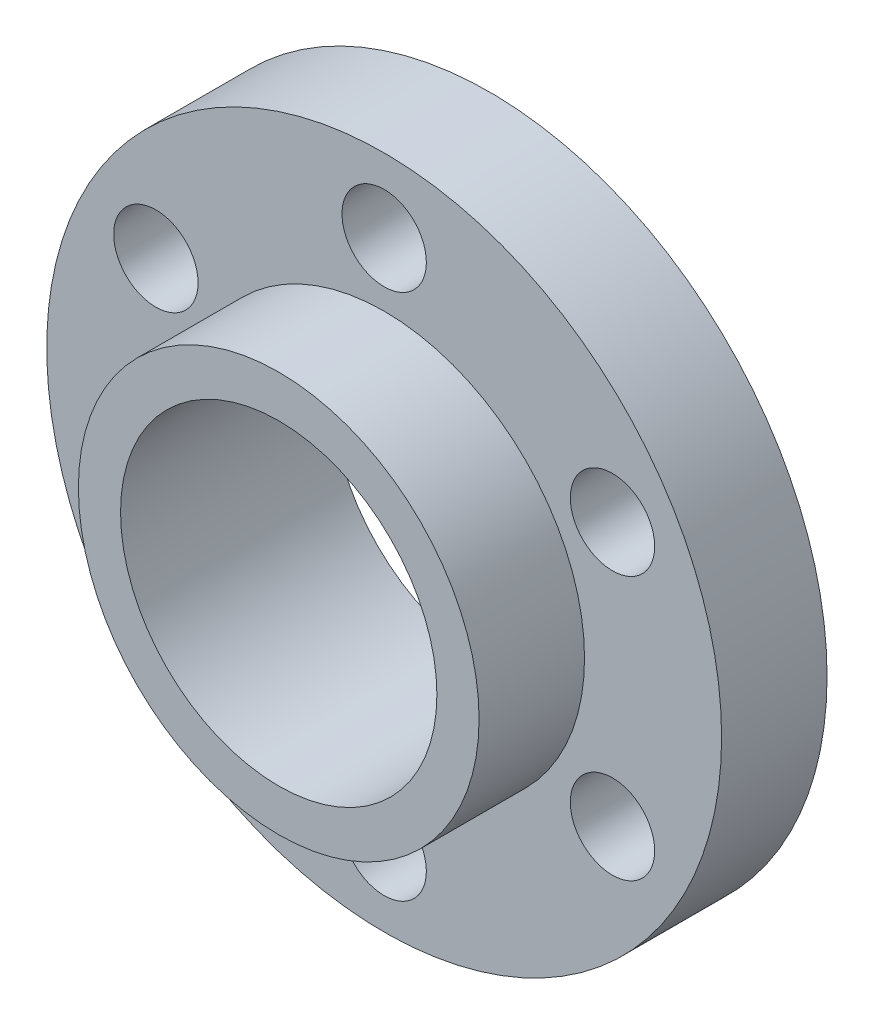
SolidWorks part; units mm, degrees
ref_plane "Front Plane" through (0, 0, 0) normal (0, 0, 1) x (1, 0, 0)
ref_plane "Top Plane" through (0, 0, 0) normal (0, 1, 0) x (1, 0, 0)
ref_plane "Right Plane" through (0, 0, 0) normal (1, 0, 0) x (0, 0, -1)
sketch "Sketch1" plane through (0, 0, 0) normal (0, 0, 1) x (1, 0, 0)
  circle A0 centre (0, 0) radius 15
  circle A1 centre (0, 0) radius 32
  dimension "D1" = 30
  dimension "D2" = 64
extrude "Boss-Extrude1" add sketch "Sketch1" along normal blind 10
sketch "Sketch2" plane through (0, 0, 10) normal (0, 0, 1) x (1, 0, 0)
  circle A0 centre (0, 0) radius 32 construction
  circle A1 centre (21.6506, 12.5) radius 4
  circle A2 centre (0, 25) radius 4
  circle A8 centre (0, 0) radius 19
  circle A9 centre (0, 0) radius 15
  circle A10 centre (21.6506, -12.5) radius 4
  circle A11 centre (0, -25) radius 4
  circle A12 centre (-21.6506, -12.5) radius 4
  circle A13 centre (-21.6506, 12.5) radius 4
  point P3 (0, 25)
  point P4 (0, 32)
  point P5 (0, 15)
  point P28 (0, 0)
  dimension "D1" = 7
  dimension "D2" = 6
extrude "Boss-Extrude2" add sketch "Sketch2" along normal blind 10 contours A8 | A9
sketch "Sketch6" plane through (0, 0, 10) normal (0, 0, 1) x (1, 0, 0)
  circle A6 centre (-21.6506, 12.5) radius 4
  circle A7 centre (0, 25) radius 4
  circle A8 centre (21.6506, 12.5) radius 4
  circle A9 centre (21.6506, -12.5) radius 4
  circle A10 centre (0, -25) radius 4
  circle A11 centre (-21.6506, -12.5) radius 4
  point P0 (0, 25)
  point P17 (0, 0)
  point P19 (0, 0)
  dimension "D1" = 6
extrude "Cut-Extrude1" cut sketch "Sketch6" against normal through all
